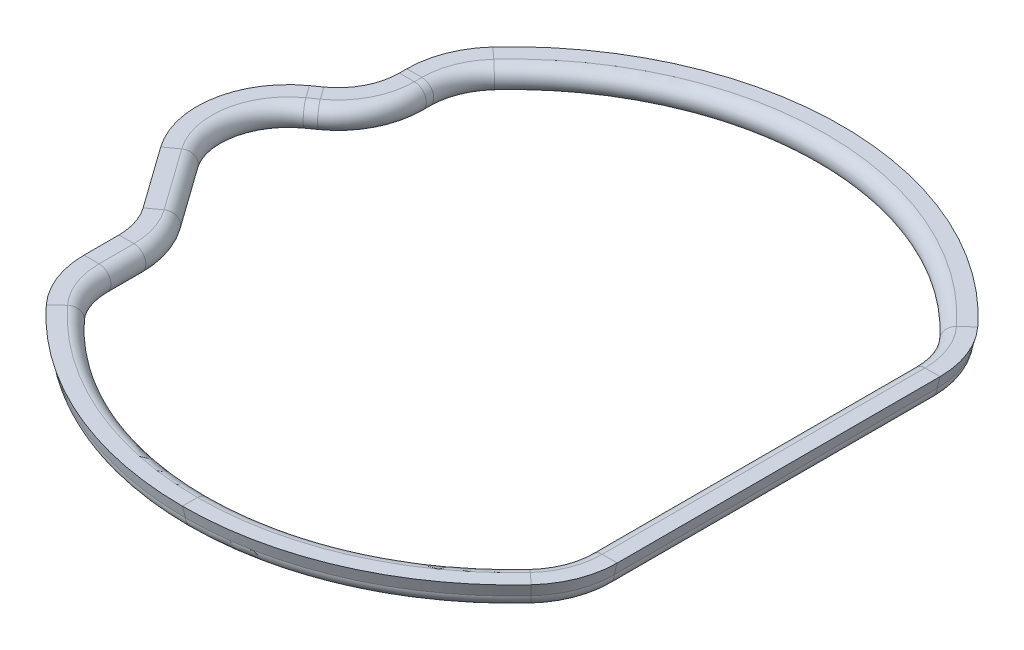
SolidWorks part; units mm, degrees
ref_plane "Vorne" through (0, 0, 0) normal (0, 0, 1) x (1, 0, 0)
ref_plane "Oben" through (0, 0, 0) normal (0, 1, 0) x (1, 0, 0)
ref_plane "Rechts" through (0, 0, 0) normal (1, 0, 0) x (0, 0, -1)
sketch "Skizze1" plane through (0, 0, 0) normal (0, 1, 0) x (1, 0, 0)
  line L0 (-69.6545, -21.5281) -> (-81.1741, -5.3932)
  line L2 (65.9318, -42.3008) -> (65.9318, 42.3008)
  line L4 (-65.9318, -42.3008) -> (-65.9318, -33.1492)
  line L5 (65.9318, -49.4954) -> (-65.9318, 49.4954) construction
  line L6 (65.9318, 49.4954) -> (-65.9318, -49.4954) construction
  line L7 (-76.518, 22.5052) -> (-74.3106, 24.0812)
  line L8 (-65.9318, 40.3584) -> (-65.9318, 42.3008)
  arc A0 (-60.6434, -55.8495) -> (60.6434, -55.8495) centre (0, 0) ccw
  arc A1 (60.6434, 55.8495) -> (-60.6434, 55.8495) centre (0, 0) ccw
  arc A2 (-60.6434, -55.8495) -> (-65.9318, -42.3008) centre (-45.9318, -42.3008) cw
  arc A3 (60.6434, -55.8495) -> (65.9318, -42.3008) centre (45.9318, -42.3008) ccw
  arc A4 (65.9318, 42.3008) -> (60.6434, 55.8495) centre (45.9318, 42.3008) ccw
  arc A5 (-60.6434, 55.8495) -> (-65.9318, 42.3008) centre (-45.9318, 42.3008) ccw
  arc A6 (-81.1741, -5.3932) -> (-76.518, 22.5052) centre (-64.8968, 6.228) cw
  arc A7 (-74.3106, 24.0812) -> (-65.9318, 40.3584) centre (-85.9318, 40.3584) ccw
  arc A8 (-69.6545, -21.5281) -> (-65.9318, -33.1492) centre (-85.9318, -33.1492) cw
  point P25 (-65.9318, 30.0633)
  dimension "D1" = 20
  dimension "D2" = 20
sketch "Skizze2" plane through (0, 0, 0) normal (1, 0, 0) x (0, 0, -1)
  line L0 (-82.4427, 3.1143) -> (-86.3846, 3.1143)
  line L1 (-86.3846, 3.1143) -> (-85.5569, 0)
  arc A0 (-85.5569, 0) -> (-82.4427, 3.1143) centre (-82.4427, 0) ccw
sweep "Austragung1" add profiles "Skizze2" path "Skizze1"
